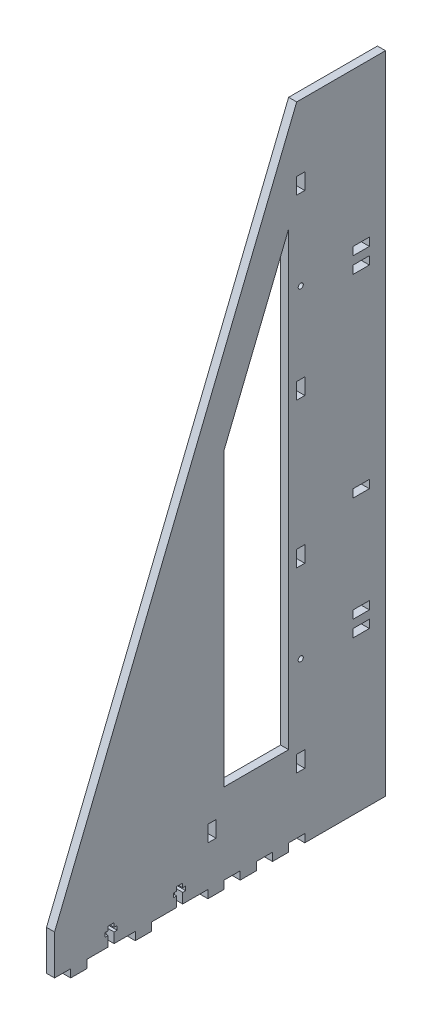
SolidWorks part; units mm, degrees
ref_plane "Front Plane" through (0, 0, 0) normal (0, 0, 1) x (1, 0, 0)
ref_plane "Top Plane" through (0, 0, 0) normal (0, 1, 0) x (1, 0, 0)
ref_plane "Right Plane" through (0, 0, 0) normal (1, 0, 0) x (0, 0, -1)
sketch "Sketch1" plane through (0, 0, 0) normal (1, 0, 0) x (0, 0, -1)
  line L0 (12.7, 0) -> (25.4, 0)
  line L1 (260.35, 0) -> (260.35, 508)
  line L2 (260.35, 508) -> (190.5, 508)
  line L3 (63.5, 0) -> (76.2, 0)
  line L4 (0, 37.7031) -> (190.5, 508)
  line L5 (120.65, 0) -> (133.35, 0)
  line L6 (184.15, 6.35) -> (196.85, 6.35)
  line L7 (184.15, 6.35) -> (184.15, 0)
  line L8 (184.15, 424.6682) -> (184.15, 69.85)
  line L9 (196.85, 6.35) -> (196.85, 0)
  line L10 (133.35, 274.0953) -> (133.35, 299.2557)
  line L11 (158.75, 0) -> (158.75, 6.35)
  line L12 (171.45, 0) -> (176.7495, 0)
  line L13 (158.75, 6.35) -> (171.45, 6.35)
  line L14 (146.05, 6.35) -> (133.35, 6.35)
  line L15 (146.05, 6.35) -> (146.05, 0)
  line L16 (0, 0) -> (0, 37.7031)
  line L17 (133.35, 6.35) -> (133.35, 0)
  line L18 (120.65, 6.35) -> (76.2, 6.35)
  line L19 (120.65, 6.35) -> (120.65, 0)
  line L20 (133.35, 299.2557) -> (184.15, 424.6682)
  line L21 (76.2, 6.35) -> (76.2, 0)
  line L22 (63.5, 6.35) -> (25.4, 6.35)
  line L23 (63.5, 6.35) -> (63.5, 0)
  line L25 (25.4, 6.35) -> (25.4, 0)
  line L26 (171.45, 0) -> (171.45, 6.35)
  line L27 (12.7, 6.35) -> (0, 6.35)
  line L28 (12.7, 6.35) -> (12.7, 0)
  line L31 (146.05, 0) -> (158.75, 0)
  line L32 (171.45, 0) -> (184.15, 0)
  line L33 (196.85, 0) -> (260.35, 0)
  line L34 (184.15, 69.85) -> (133.35, 69.85)
  line L35 (133.35, 69.85) -> (133.35, 274.0953)
  dimension "D2" = 69.85
  dimension "D3" = 508
  dimension "D4" = 63.5
  dimension "D5" = 63.5
  dimension "D6" = 12.7
  dimension "D7" = 6.35
  dimension "D8" = 6.35
  dimension "D9" = 12.7
  dimension "D10" = 12.7
  dimension "D11" = 12.7
  dimension "D12" = 12.7
  dimension "D13" = 6.35
  dimension "D14" = 6.35
  dimension "D15" = 12.7
  dimension "D16" = 44.45
  dimension "D17" = 12.7
  dimension "D18" = 6.35
  dimension "D19" = 38.1
  dimension "D20" = 12.7
  dimension "D21" = 6.35
  dimension "D22" = 25.4
  dimension "D24" = 50.8
extrude "Boss-Extrude1" add sketch "Sketch1" along normal blind 6.35 contours L9 L33 L1 L2 L4 L27 L28 L0 L25 L22 L23 L3 L21 L18 L19 L5 L17 L14 L15 L31 L11 L13 L26 L12 L32 L7 L6 L34 L35 L10 L20 L8
sketch "Sketch3" plane through (6.35, 0, 0) normal (1, 0, 0) x (0, 0, -1)
  line L0 (25.4, 6.35) -> (25.4, 0) construction
  line L1 (63.5, 6.35) -> (63.5, 0) construction
  line L2 (76.2, 6.35) -> (76.2, 0) construction
  line L3 (120.65, 6.35) -> (120.65, 0) construction
  line L4 (49.2125, 17.4625) -> (49.2125, 14.2875)
  line L5 (196.85, 6.35) -> (196.85, 0) construction
  line L6 (260.35, 0) -> (260.35, 508) construction
  line L8 (46.8313, 6.35) -> (42.0688, 6.35)
  line L9 (25.4, 6.35) -> (25.4, 0) construction
  line L10 (103.1875, 17.4625) -> (103.1875, 14.2875)
  line L11 (42.0688, 6.35) -> (42.0688, 14.2875)
  line L12 (46.8313, 14.2875) -> (49.2125, 14.2875)
  line L13 (100.8063, 6.35) -> (96.0438, 6.35)
  line L14 (96.0438, 6.35) -> (96.0438, 14.2875)
  line L15 (100.8063, 14.2875) -> (103.1875, 14.2875)
  line L16 (100.8063, 20.6375) -> (96.0438, 20.6375)
  line L17 (96.0438, 17.4625) -> (96.0438, 20.6375)
  line L18 (96.0438, 17.4625) -> (93.6625, 17.4625)
  line L19 (46.8313, 20.6375) -> (42.0688, 20.6375)
  line L20 (42.0688, 17.4625) -> (42.0688, 20.6375)
  line L21 (42.0688, 17.4625) -> (39.6875, 17.4625)
  line L22 (96.0438, 14.2875) -> (93.6625, 14.2875)
  line L23 (42.0688, 14.2875) -> (39.6875, 14.2875)
  line L24 (39.6875, 17.4625) -> (39.6875, 14.2875)
  line L25 (93.6625, 17.4625) -> (93.6625, 14.2875)
  line L26 (46.8313, 17.4625) -> (49.2125, 17.4625)
  line L27 (46.8313, 17.4625) -> (46.8313, 20.6375)
  line L28 (100.8063, 17.4625) -> (103.1875, 17.4625)
  line L29 (46.8313, 6.35) -> (46.8313, 14.2875)
  line L30 (100.8063, 17.4625) -> (100.8063, 20.6375)
  line L31 (100.8063, 14.2875) -> (100.8063, 6.35)
  line L32 (120.65, 6.35) -> (76.2, 6.35) construction
  line L33 (76.2, 6.35) -> (76.2, 0) construction
  point P0 (25.4, 3.175)
  point P5 (76.2, 3.175)
  point P8 (120.65, 3.175)
  point P13 (196.85, 3.175)
  dimension "D1" = 38.1
  dimension "D2" = 44.45
  dimension "D3" = 63.5
  dimension "D4" = 16.6688
  dimension "D5" = 2.3813
  dimension "D6" = 2.3813
  dimension "D7" = 3.175
  dimension "D8" = 3.175
  dimension "D9" = 3.175
  dimension "D10" = 0
  dimension "D11" = 19.8438
  dimension "D12" = 2.3813
  dimension "D13" = 4.7625
extrude "Cut-Extrude1" cut sketch "Sketch3" against normal blind 6.35
sketch "Sketch5" plane through (6.35, 0, 0) normal (1, 0, 0) x (0, 0, -1)
  line L0 (196.85, 6.35) -> (196.85, 0) construction
  line L1 (260.35, 0) -> (260.35, 508) construction
  line L2 (244.5941, 254) -> (209.4994, 254)
  line L3 (196.85, 50.8) -> (190.5, 50.8)
  line L4 (196.85, 50.8) -> (196.85, 63.5)
  line L5 (196.85, 63.5) -> (190.5, 63.5)
  line L6 (190.5, 50.8) -> (190.5, 63.5)
  line L7 (196.85, 190.5) -> (190.5, 190.5)
  line L8 (196.85, 190.5) -> (196.85, 203.2)
  line L9 (196.85, 203.2) -> (190.5, 203.2)
  line L10 (190.5, 190.5) -> (190.5, 203.2)
  line L11 (196.85, 0) -> (260.35, 0) construction
  line L12 (234.95, 374.65) -> (234.95, 368.3)
  line L13 (247.65, 127) -> (234.95, 127)
  line L14 (247.65, 127) -> (247.65, 120.65)
  line L15 (247.65, 120.65) -> (234.95, 120.65)
  line L16 (234.95, 127) -> (234.95, 120.65)
  line L17 (247.65, 133.35) -> (234.95, 133.35)
  line L18 (247.65, 133.35) -> (247.65, 139.7)
  line L19 (247.65, 139.7) -> (234.95, 139.7)
  line L20 (234.95, 133.35) -> (234.95, 139.7)
  line L21 (247.65, 368.3) -> (234.95, 368.3)
  line L22 (247.65, 374.65) -> (247.65, 368.3)
  line L23 (247.65, 374.65) -> (234.95, 374.65)
  line L24 (234.95, 381) -> (234.95, 387.35)
  line L25 (247.65, 387.35) -> (234.95, 387.35)
  line L26 (247.65, 381) -> (247.65, 387.35)
  line L27 (247.65, 381) -> (234.95, 381)
  line L28 (190.5, 317.5) -> (190.5, 304.8)
  line L29 (196.85, 304.8) -> (190.5, 304.8)
  line L30 (196.85, 317.5) -> (196.85, 304.8)
  line L31 (196.85, 317.5) -> (190.5, 317.5)
  line L32 (190.5, 457.2) -> (190.5, 444.5)
  line L33 (196.85, 444.5) -> (190.5, 444.5)
  line L34 (196.85, 457.2) -> (196.85, 444.5)
  line L35 (196.85, 457.2) -> (190.5, 457.2)
  circle A0 centre (193.675, 127) radius 2
  circle A1 centre (193.675, 381) radius 2
  point P0 (196.85, 3.175)
  dimension "D11" = 4
  dimension "D1" = 63.5
  dimension "D2" = 254
  dimension "D3" = 6.35
  dimension "D4" = 63.5
  dimension "D5" = 63.5
  dimension "D6" = 6.35
  dimension "D7" = 63.5
  dimension "D8" = 63.5
  dimension "D9" = 12.7
  dimension "D10" = 12.7
  dimension "D12" = 63.5
  dimension "D13" = 12.7
  dimension "D14" = 12.7
  dimension "D15" = 12.7
  dimension "D16" = 12.7
  dimension "D17" = 6.35
  dimension "D18" = 6.35
  dimension "D19" = 6.35
  dimension "D20" = 0
extrude "Cut-Extrude2" cut sketch "Sketch5" against normal blind 6.35 contours L34 L33 L32 L35 | L25 L24 L27 L26 | L23 L12 L21 L22 | A1 | L31 L28 L29 L30 | L8 L9 L10 L7 | A0 | L5 L6 L3 L4 | L15 L16 L13 L14 | L17 L20 L19 L18
sketch "Sketch6" plane through (6.35, 0, 0) normal (1, 0, 0) x (0, 0, -1)
  line L0 (120.65, 0) -> (133.35, 0) construction
  line L1 (120.65, 38.1) -> (127, 38.1)
  line L2 (120.65, 38.1) -> (120.65, 50.8)
  line L3 (120.65, 50.8) -> (127, 50.8)
  line L4 (127, 38.1) -> (127, 50.8)
  dimension "D1" = 38.1
  dimension "D2" = 12.7
  dimension "D3" = 6.35
extrude "Cut-Extrude3" cut sketch "Sketch6" against normal blind 6.35
sketch "Sketch7" plane through (6.35, 0, 0) normal (1, 0, 0) x (0, 0, -1)
  line L0 (196.85, 0) -> (260.35, 0) construction
  line L1 (247.65, 215.9) -> (234.95, 215.9)
  line L2 (247.65, 215.9) -> (247.65, 222.25)
  line L3 (247.65, 222.25) -> (234.95, 222.25)
  line L4 (234.95, 215.9) -> (234.95, 222.25)
  dimension "D1" = 6.35
  dimension "D2" = 215.9
extrude "Cut-Extrude4" cut sketch "Sketch7" against normal blind 6.35
